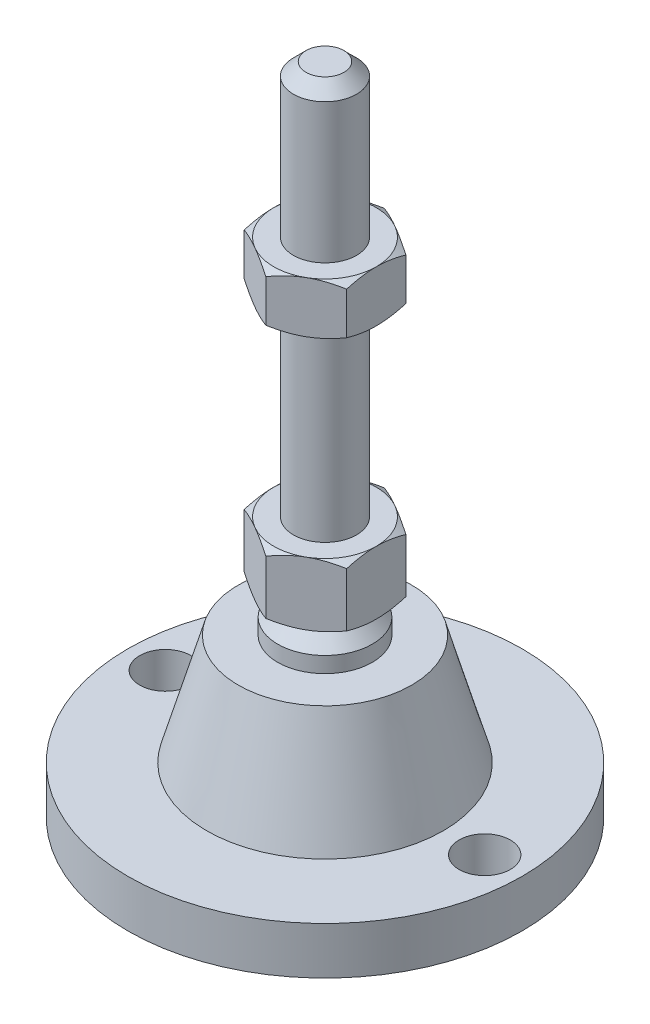
SolidWorks part; units mm, degrees
ref_plane "Спереди" through (0, 0, 0) normal (0, 0, 1) x (1, 0, 0)
ref_plane "Сверху" through (0, 0, 0) normal (0, 1, 0) x (1, 0, 0)
ref_plane "Справа" through (0, 0, 0) normal (1, 0, 0) x (0, 0, -1)
sketch "Эскиз1" plane through (0, 0, 0) normal (0, 0, 1) x (1, 0, 0)
  line L0 (0, 0) -> (-25, 0)
  line L3 (-25, 0) -> (-25, 6)
  line L12 (-4, 33) -> (-4, 81.4)
  line L13 (-4, 81.4) -> (-2.4, 83)
  line L14 (-2.4, 83) -> (0, 83)
  line L15 (0, 83) -> (0, 0) construction
  line L16 (-25, 6) -> (-15, 6)
  line L17 (0, 0) -> (0, 83)
  line L18 (0, 0) -> (0, -7.9595) construction
  line L19 (-4, 33) -> (-4, 25)
  line L21 (-6, 20) -> (-11, 20)
  line L22 (-15, 6) -> (-11, 20)
  line L23 (-6, 20) -> (-6, 22)
  line L24 (-6, 22) -> (-4, 24)
  line L25 (-4, 24) -> (-4, 25)
  line L26 (-4, 33) -> (0, 33) construction
  point P1 (-5.1467, 20)
  point P8 (-4, 57.2)
  point P18 (-5.0675, 20)
  dimension "D1" = 8
  dimension "D2" = 5
  dimension "D3" = 8
  dimension "D4" = 50
  dimension "D5" = 20
  dimension "D6" = 1.6
  dimension "D7" = 45
  dimension "D8" = 14
  dimension "D9" = 10
  dimension "D10" = 50
  dimension "D11" = 6
  dimension "D12" = 4
  dimension "D13" = 6
  dimension "D14" = 135
  dimension "D15" = 2
revolve "Повернуть1" add sketch "Эскиз1" angle 360 about L17
ref_plane "Плоскость2" through (0, 25, 0) normal (0, 1, 0) x (1, 0, 0)
sketch "Эскиз2" plane through (0, 25, 0) normal (0, 1, 0) x (1, 0, 0)
  line L1 (0, 7.5056) -> (-6.5, 3.7528)
  line L2 (-6.5, 3.7528) -> (-6.5, -3.7528)
  line L3 (-6.5, -3.7528) -> (0, -7.5056)
  line L4 (0, -7.5056) -> (6.5, -3.7528)
  line L5 (6.5, -3.7528) -> (6.5, 3.7528)
  line L6 (6.5, 3.7528) -> (0, 7.5056)
  circle A0 centre (0, 0) radius 6.5 construction
  dimension "D1" = 13
extrude "Бобышка-Вытянуть1" add sketch "Эскиз2" along normal up to vertex (8 mm away) up to point (-4, 33, 0)
ref_plane "Плоскость1" through (0, 57.2, 0) normal (0, 1, 0) x (1, 0, 0)
sketch "Эскиз3" plane through (0, 57.2, 0) normal (0, 1, 0) x (1, 0, 0)
  line L6 (6.5, 3.7528) -> (0, 7.5056)
  line L7 (0, 7.5056) -> (-6.5, 3.7528)
  line L8 (-6.5, 3.7528) -> (-6.5, -3.7528)
  line L9 (-6.5, -3.7528) -> (0, -7.5056)
  line L10 (0, -7.5056) -> (6.5, -3.7528)
  line L11 (6.5, -3.7528) -> (6.5, 3.7528)
  line L12 (6.5, 3.7528) -> (0, 7.5056)
  line L13 (0, 7.5056) -> (-6.5, 3.7528)
  line L14 (-6.5, 3.7528) -> (-6.5, -3.7528)
  line L15 (-6.5, -3.7528) -> (0, -7.5056)
  line L16 (0, -7.5056) -> (6.5, -3.7528)
  line L17 (6.5, -3.7528) -> (6.5, 3.7528)
  dimension "D1" = 0
extrude "Бобышка-Вытянуть2" add sketch "Эскиз3" along normal blind 6.5
sketch "Эскиз4" plane through (0, 0, 0) normal (0, 0, 1) x (1, 0, 0)
  line L0 (-6.5, 63.7) -> (-12.1292, 60.45)
  line L1 (-12.1292, 60.45) -> (-12.1292, 63.7)
  line L2 (-12.1292, 63.7) -> (-6.5, 63.7)
  line L3 (-12.1292, 60.45) -> (-6.5, 57.2)
  line L4 (50, 57.2) -> (-50, 57.2) construction
  line L5 (-6.5, 57.2) -> (-12.1292, 57.2)
  line L6 (-12.1292, 57.2) -> (-12.1292, 60.45)
  line L7 (-6.5, 63.7) -> (-6.5, 57.2) construction
  line L8 (-6.5, 33) -> (-13.4282, 33)
  line L9 (-13.4282, 33) -> (-13.4282, 29)
  line L10 (-13.4282, 29) -> (-6.5, 33)
  line L11 (-6.5, 25) -> (-13.4282, 29)
  line L12 (-13.4282, 29) -> (-13.4282, 25)
  line L13 (-13.4282, 25) -> (-6.5, 25)
  line L14 (0, 83) -> (0, 96.3793) construction
  line L15 (50, 25) -> (-50, 25) construction
  dimension "D1" = 30
  dimension "D2" = 30
revolve "Вырез-Повернуть2" cut sketch "Эскиз4" angle 360 about L14
sketch "Эскиз5" plane through (0, 6, 0) normal (0, 1, 0) x (1, 0, 0)
  line L0 (20.25, 0) -> (-20.25, 0) construction
  circle A0 centre (-20.25, 0) radius 3.25
  circle A1 centre (20.25, 0) radius 3.25
  circle A2 centre (0, 0) radius 25 construction
  dimension "D1" = 6.5
  dimension "D2" = 1.5
extrude "Вырез-Вытянуть1" cut sketch "Эскиз5" against normal through all
